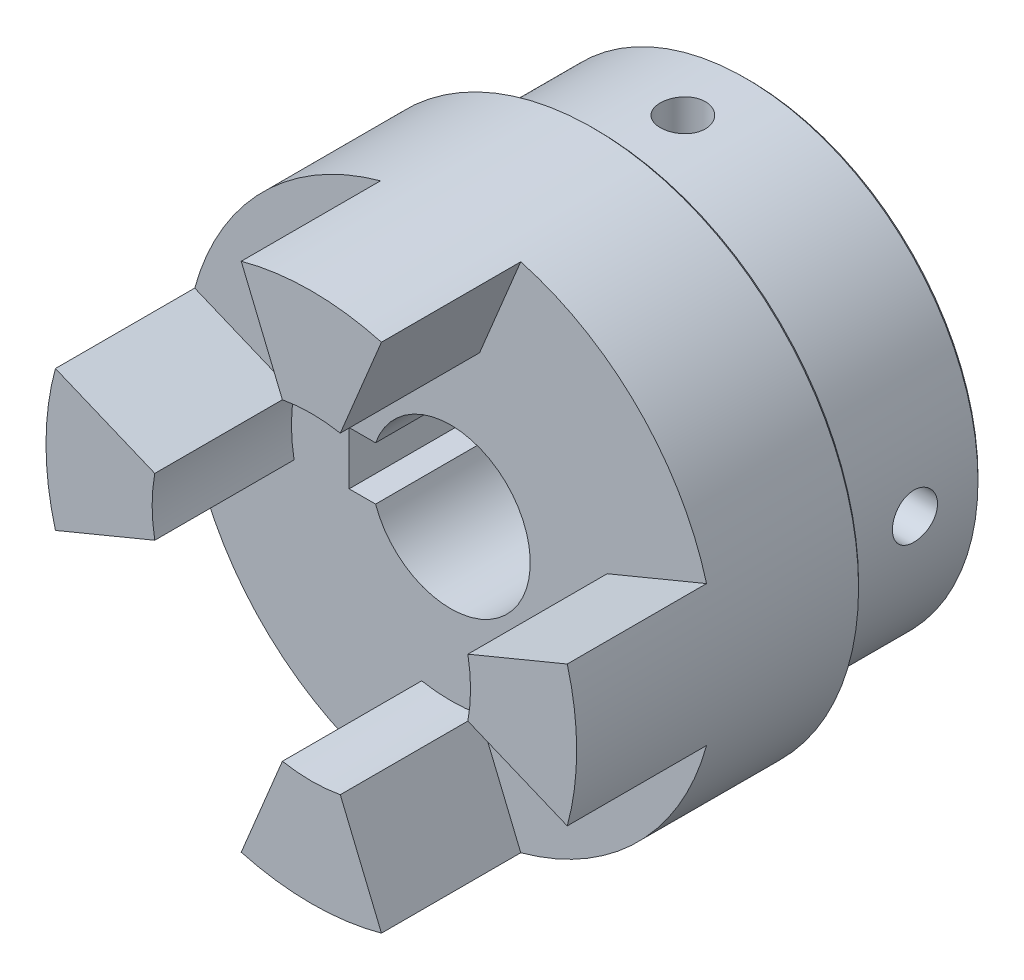
SolidWorks part; units mm, degrees
ref_plane "Front Plane" through (0, 0, 0) normal (0, 0, 1) x (1, 0, 0)
ref_plane "Top Plane" through (0, 0, 0) normal (0, 1, 0) x (1, 0, 0)
ref_plane "Right Plane" through (0, 0, 0) normal (1, 0, 0) x (0, 0, -1)
sketch "Sketch3" plane through (0, 0, 0) normal (1, 0, 0) x (0, 0, -1)
  line L0 (-22.5, 0) -> (22.5, 0) construction
  line L1 (22.5, 0) -> (22.5, 34.5)
  line L2 (22, 35) -> (-0.5, 35)
  line L3 (-0.5, 35) -> (-0.5, 39.5)
  line L4 (-1, 40) -> (-22.5, 40)
  line L5 (-22.5, 40) -> (-22.5, 0)
  line L6 (22.5, 0) -> (-22.5, 0)
  line L7 (-0.5, 39.5) -> (-1, 40)
  line L8 (22.5, 34.5) -> (22, 35)
  point P0 (-0.5, 40)
  point P4 (0, 0)
  point P6 (22.5, 35)
  dimension "D1" = 45
  dimension "D2" = 23
  dimension "D3" = 35
  dimension "D4" = 40
revolve "Revolve2" add sketch "Sketch3" angle 360 about L0
sketch "Sketch5" plane through (0, 0, 22.5) normal (0, 0, 1) x (1, 0, 0)
  line L0 (0, 0) -> (0, 52.6426) construction
  line L1 (-4.365, 23.5997) -> (-10.5694, 38.5783)
  line L2 (4.365, 23.5997) -> (10.5694, 38.5783)
  line L3 (-4.365, 23.5997) -> (4.365, 23.5997) construction
  circle A0 centre (0, 0) radius 40 construction
  arc A1 (10.5694, 38.5783) -> (-10.5694, 38.5783) centre (0, 0) ccw
  arc A2 (4.365, 23.5997) -> (-4.365, 23.5997) centre (0, 0) ccw
  dimension "D1" = 48
  dimension "D2" = 22.5
  dimension "D3" = 45
  dimension "D4" = 8.73
extrude "Boss-Extrude1" add sketch "Sketch5" along normal blind 21
pattern_circular "CirPattern1" count 4 over 360 about axis through (0, 0, 0) along (0, 0, 1) of "Boss-Extrude1"
sketch "Sketch6" plane through (0, 0, 22.5) normal (0, 0, 1) x (1, 0, 0)
  line L1 (-15.3, 4) -> (-8.7, 4)
  line L2 (-15.3, 4) -> (-15.3, -4)
  line L3 (-15.3, -4) -> (-8.7, -4)
  line L4 (-8.7, 4) -> (-8.7, -4)
  line L5 (-15.3, 4) -> (-8.7, -4) construction
  line L6 (-15.3, -4) -> (-8.7, 4) construction
  circle A0 centre (0, 0) radius 12
  point P3 (-12, 0)
  dimension "D1" = 24
  dimension "D2" = 8
  dimension "D3" = 15.3
extrude "Cut-Extrude2" cut sketch "Sketch6" against normal through all contours L1 A0 L3 L4 | A0 L1 L2 L3 | L3 A0 L1 L4
hole_wizard "Tap Drill for M8x1.25 Tap2" positions "Sketch11" profile "Sketch12" hole size "M8x1.25" standard "ANSI Metric"
sketch "Sketch11" plane through (0, 0, 0) normal (1, 0, 0) x (0, 0, -1)
  line L0 (22.5, -34.5) -> (22.5, 34.5) construction
  point P0 (12.5, 0)
  dimension "D1" = 10
sketch "Sketch12" plane through (0, 0, -12.5) normal (0, 1, 0) x (0, 0, 1)
  line L0 (0, 0) -> (0, 35)
  line L1 (0, 35) -> (3.4, 35)
  line L2 (3.4, 35) -> (3.4, 0)
  line L5 (3.4, 0) -> (0, 0)
  line L11 (0, -6.35) -> (0, 107.95) construction
  dimension "Thru Hole Dia." = 6.8
  dimension "Thru Hole Depth" = 35
pattern_circular "CirPattern2" count 2 over 90 about axis through (0, 0, 22.5) along (0, 0, 1) of "Tap Drill for M8x1.25 Tap2"
